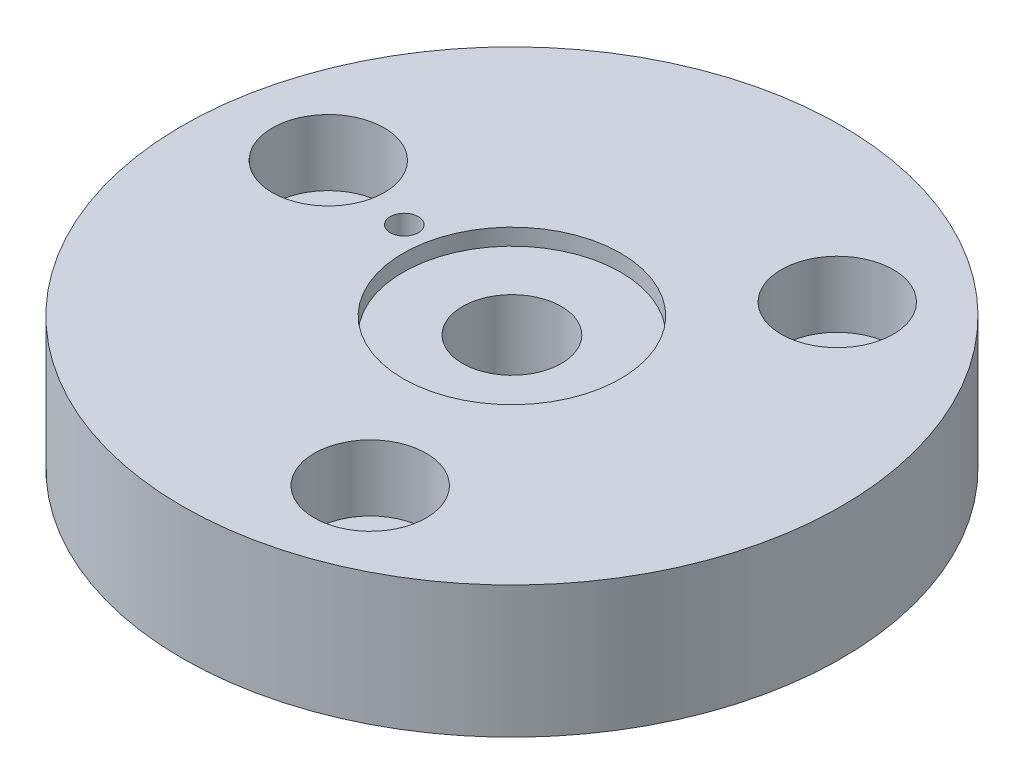
SolidWorks part; units mm, degrees
ref_plane "Plan de face" through (0, 0, 0) normal (0, 0, 1) x (1, 0, 0)
ref_plane "Plan de dessus" through (0, 0, 0) normal (0, 1, 0) x (1, 0, 0)
ref_plane "Plan de droite" through (0, 0, 0) normal (1, 0, 0) x (0, 0, -1)
sketch "Esquisse1" plane through (0, 0, 0) normal (0, 1, 0) x (1, 0, 0)
  line L0 (0, 0) -> (-42.916, 8.1422) construction
  line L1 (-42.916, 8.1422) -> (-81.1333, 15.3929) construction
  circle A0 centre (0, 0) radius 100
  circle A1 centre (0, 0) radius 41 construction
  circle A2 centre (-40.3117, 7.6481) radius 4.25
  circle A3 centre (0, 0) radius 70 construction
  circle A4 centre (-68.9473, 13.0809) radius 8
  circle A5 centre (45.802, 53.1696) radius 8
  circle A6 centre (23.1452, -66.2505) radius 8
  point P18 (0, 0)
  dimension "D1" = 3
  dimension "D2" = 8.5
  dimension "D3" = 16
extrude "Boss.-Extru.1" add sketch "Esquisse1" against normal blind 40
sketch "Esquisse3" plane through (0, 0, 0) normal (0, 1, 0) x (1, 0, 0)
  circle A2 centre (0, 0) radius 5
extrude "Enlèv. mat.-Extru.2" cut sketch "Esquisse3" against normal through all contours A2
sketch "Esquisse5" plane through (0, 0, 0) normal (0, 1, 0) x (1, 0, 0)
  circle A0 centre (0, 0) radius 15
extrude "Enlèv. mat.-Extru.3" cut sketch "Esquisse5" against normal blind 30
sketch "Esquisse6" plane through (0, 0, 0) normal (0, 1, 0) x (1, 0, 0)
  circle A0 centre (0, 0) radius 33
extrude "Enlèv. mat.-Extru.4" cut sketch "Esquisse6" against normal blind 5
sketch "Esquisse7" plane through (0, 0, 0) normal (0, 1, 0) x (1, 0, 0)
  line L0 (0, 0) -> (-40.3117, 7.6481) construction
  line L1 (-40.3117, 7.6481) -> (-76.3825, 14.4916) construction
  line L2 (-76.3825, 14.4916) -> (-84.3209, 15.9977) construction
  circle A0 centre (0, 0) radius 70
sketch "Esquisse8" plane through (0, 0, 0) normal (0, 1, 0) x (1, 0, 0)
  line L0 (-40.3117, 7.6481) -> (-76.3825, 14.4916) construction
  circle A0 centre (-68.7732, 13.0479) radius 17
  circle A1 centre (0, 0) radius 70 construction
extrude "Enlèv. mat.-Extru.5" cut sketch "Esquisse8" against normal blind 20
pattern_circular "Répétition circulaire1" count 3 every 120 about axis through (0, 0, 0) along (0, 1, 0) of "Enlèv. mat.-Extru.5"
